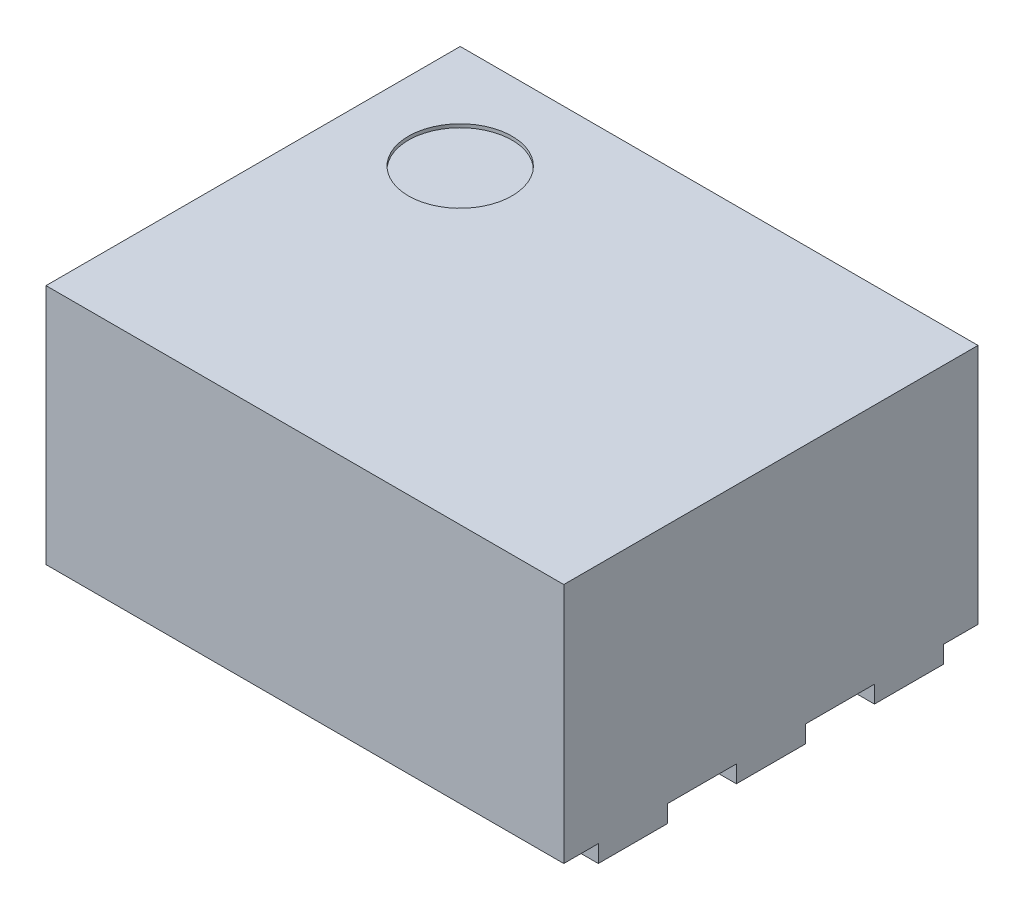
SolidWorks part; units mm, degrees
ref_plane "Front Plane" through (0, 0, 0) normal (0, 0, 1) x (1, 0, 0)
ref_plane "Top Plane" through (0, 0, 0) normal (0, 1, 0) x (1, 0, 0)
ref_plane "Right Plane" through (0, 0, 0) normal (1, 0, 0) x (0, 0, -1)
sketch "Sketch1" plane through (0, 0, 0) normal (0, 1, 0) x (1, 0, 0)
  line L1 (-0.75, 0.6) -> (0.75, 0.6)
  line L2 (-0.75, 0.6) -> (-0.75, -0.6)
  line L3 (-0.75, -0.6) -> (0.75, -0.6)
  line L4 (0.75, 0.6) -> (0.75, -0.6)
  line L5 (-0.75, 0.6) -> (0.75, -0.6) construction
  line L6 (-0.75, -0.6) -> (0.75, 0.6) construction
  point P0 (0, 0)
  dimension "D1" = 1.5
  dimension "D2" = 1.2
extrude "Boss-Extrude1" add sketch "Sketch1" along normal blind 0.7
sketch "Sketch2" plane through (0, 0, 0) normal (0, -1, 0) x (1, 0, 0)
  line L0 (-0.75, -0.6) -> (-0.75, 0.6) construction
  line L1 (-0.75, 0.5) -> (-0.46, 0.5)
  line L2 (-0.75, 0.5) -> (-0.75, 0.3)
  line L3 (-0.75, 0.3) -> (-0.46, 0.3)
  line L4 (-0.46, 0.5) -> (-0.46, 0.3)
  line L5 (0, 0) -> (-0.75, 0) construction
  line L6 (-0.235, -0.425) -> (0.235, -0.425)
  line L7 (-0.235, -0.425) -> (-0.235, 0.425)
  line L8 (-0.235, 0.425) -> (0.235, 0.425)
  line L9 (0.235, -0.425) -> (0.235, 0.425)
  line L10 (-0.235, -0.425) -> (0.235, 0.425) construction
  line L11 (-0.235, 0.425) -> (0.235, -0.425) construction
  line L12 (-0.75, -0.3) -> (-0.46, -0.3)
  line L13 (-0.75, 0.1) -> (-0.46, 0.1)
  line L14 (-0.75, 0.1) -> (-0.75, -0.1)
  line L15 (-0.75, -0.1) -> (-0.46, -0.1)
  line L16 (-0.46, 0.1) -> (-0.46, -0.1)
  line L17 (-0.46, -0.5) -> (-0.46, -0.3)
  line L18 (-0.75, -0.5) -> (-0.46, -0.5)
  line L19 (-0.75, -0.5) -> (-0.75, -0.3)
  line L20 (0, 0) -> (0, 0.6) construction
  line L21 (-0.75, 0.6) -> (0.75, 0.6) construction
  line L22 (0.75, -0.5) -> (0.75, -0.3)
  line L23 (0.75, -0.5) -> (0.46, -0.5)
  line L24 (0.46, -0.5) -> (0.46, -0.3)
  line L25 (0.75, -0.3) -> (0.46, -0.3)
  line L26 (0.75, -0.1) -> (0.46, -0.1)
  line L27 (0.46, 0.1) -> (0.46, -0.1)
  line L28 (0.75, 0.1) -> (0.46, 0.1)
  line L29 (0.75, 0.1) -> (0.75, -0.1)
  line L30 (0.75, 0.3) -> (0.46, 0.3)
  line L31 (0.46, 0.5) -> (0.46, 0.3)
  line L32 (0.75, 0.5) -> (0.46, 0.5)
  line L33 (0.75, 0.5) -> (0.75, 0.3)
  point P6 (0, 0)
  dimension "D1" = 0.4
  dimension "D2" = 0.29
  dimension "D3" = 0.2
  dimension "D4" = 0.47
  dimension "D5" = 0.85
extrude "Boss-Extrude2" add sketch "Sketch2" along normal blind 0.05
sketch "Sketch3" plane through (0, 0.7, 0) normal (0, 1, 0) x (1, 0, 0)
  line L0 (0.75, 0.6) -> (-0.75, 0.6) construction
  line L1 (-0.75, 0.6) -> (-0.75, -0.6) construction
  circle A0 centre (-0.45, 0.3) radius 0.15
  dimension "D1" = 0.3
  dimension "D3" = 0.3
  dimension "D2" = 0.3
extrude "Cut-Extrude1" cut sketch "Sketch3" against normal blind 0.01
